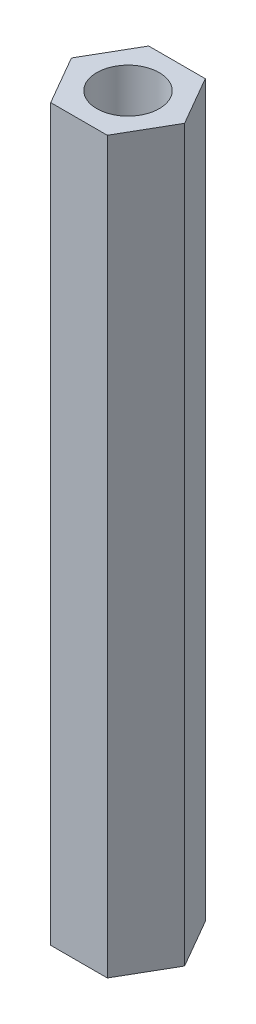
SolidWorks part; units mm, degrees
ref_plane "前视基准面" through (0, 0, 0) normal (0, 0, 1) x (1, 0, 0)
ref_plane "上视基准面" through (0, 0, 0) normal (0, 1, 0) x (1, 0, 0)
ref_plane "右视基准面" through (0, 0, 0) normal (1, 0, 0) x (0, 0, -1)
other "Configuration Table"
sketch "草图1" plane through (0, 0, 0) normal (0, 1, 0) x (1, 0, 0)
  line L1 (2.7135, 0) -> (1.3568, 2.35)
  line L2 (1.3568, 2.35) -> (-1.3568, 2.35)
  line L3 (-1.3568, 2.35) -> (-2.7135, 0)
  line L4 (-2.7135, 0) -> (-1.3568, -2.35)
  line L5 (-1.3568, -2.35) -> (1.3568, -2.35)
  line L6 (1.3568, -2.35) -> (2.7135, 0)
  circle A0 centre (0, 0) radius 2.35 construction
  circle A1 centre (0, 0) radius 1.5
  dimension "D1" = 4.7
extrude "凸台-拉伸1" add sketch "草图1" along normal blind 35
